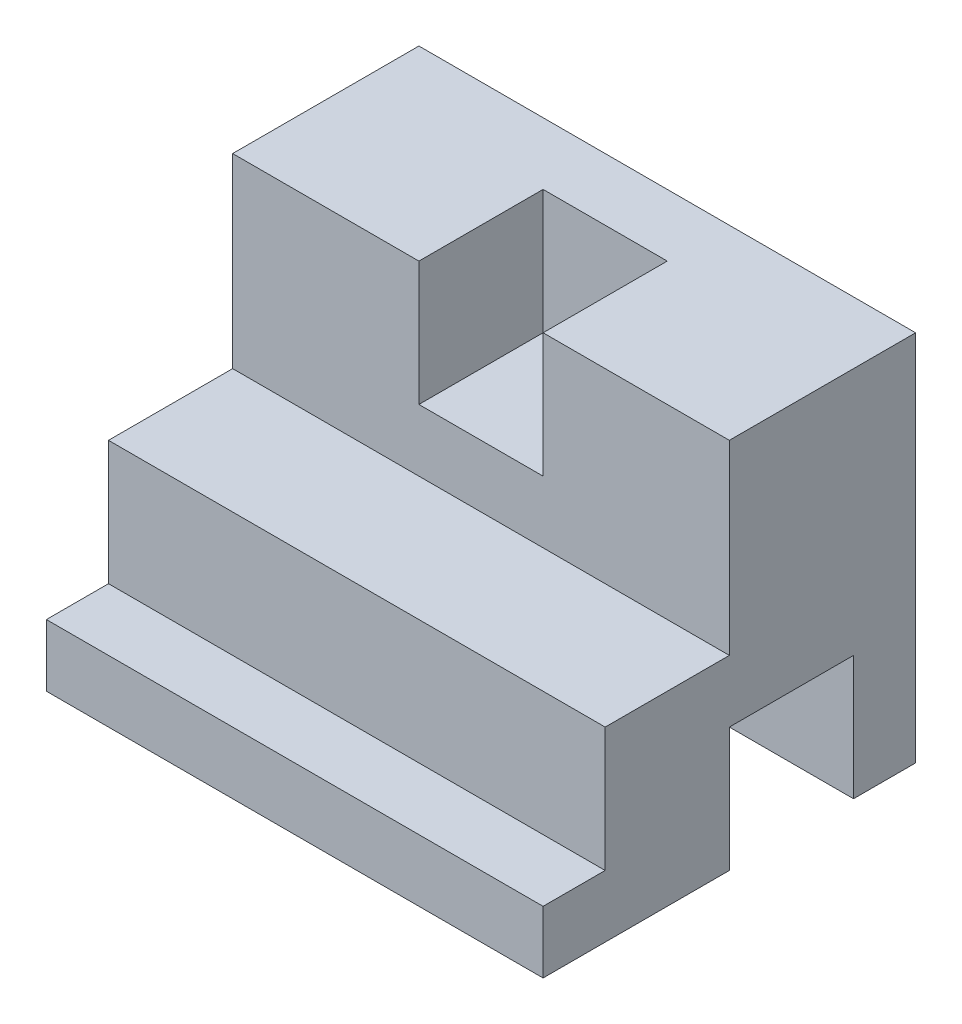
SolidWorks part; units mm, degrees
ref_plane "Front Plane" through (0, 0, 0) normal (0, 0, 1) x (1, 0, 0)
ref_plane "Top Plane" through (0, 0, 0) normal (0, 1, 0) x (1, 0, 0)
ref_plane "Right Plane" through (0, 0, 0) normal (1, 0, 0) x (0, 0, -1)
sketch "Sketch1" plane through (0, 0, 0) normal (0, 0, 1) x (1, 0, 0)
  line L1 (0, 0) -> (203.2, 0)
  line L2 (0, 0) -> (0, 152.4)
  line L3 (0, 152.4) -> (203.2, 152.4)
  line L4 (203.2, 0) -> (203.2, 152.4)
  dimension "D1" = 152.4
  dimension "D2" = 203.2
extrude "Boss-Extrude1" add sketch "Sketch1" against normal blind 152.4
sketch "Sketch2" plane through (203.2, 0, 0) normal (1, 0, 0) x (0, 0, -1)
  line L0 (0, 25.4) -> (25.4, 25.4)
  line L1 (0, 0) -> (0, 152.4) construction
  line L2 (25.4, 25.4) -> (25.4, 76.2)
  line L3 (25.4, 76.2) -> (76.2, 76.2)
  line L4 (76.2, 76.2) -> (76.2, 152.4)
  line L5 (152.4, 152.4) -> (0, 152.4) construction
  line L6 (76.2, 152.4) -> (0, 152.4)
  line L7 (0, 152.4) -> (0, 25.4)
  line L8 (76.2, 0) -> (76.2, 50.8)
  line L9 (152.4, 0) -> (0, 0) construction
  line L10 (76.2, 50.8) -> (127, 50.8)
  line L11 (127, 50.8) -> (127, 0)
  line L12 (127, 0) -> (76.2, 0)
  dimension "D1" = 127
  dimension "D2" = 25.4
  dimension "D3" = 50.8
  dimension "D4" = 50.8
  dimension "D5" = 50.8
  dimension "D6" = 50.8
extrude "Cut-Extrude1" cut sketch "Sketch2" against normal through all
sketch "Sketch3" plane through (0, 152.4, 0) normal (0, 1, 0) x (1, 0, 0)
  line L7 (0, 76.2) -> (203.2, 76.2) construction
  line L8 (76.2, 76.2) -> (127, 76.2)
  line L9 (76.2, 76.2) -> (76.2, 127)
  line L10 (76.2, 127) -> (127, 127)
  line L11 (127, 76.2) -> (127, 127)
  line L12 (203.2, 152.4) -> (203.2, 76.2) construction
  dimension "D1" = 50.8
  dimension "D2" = 50.8
  dimension "D3" = 76.2
extrude "Cut-Extrude2" cut sketch "Sketch3" against normal blind 50.8
